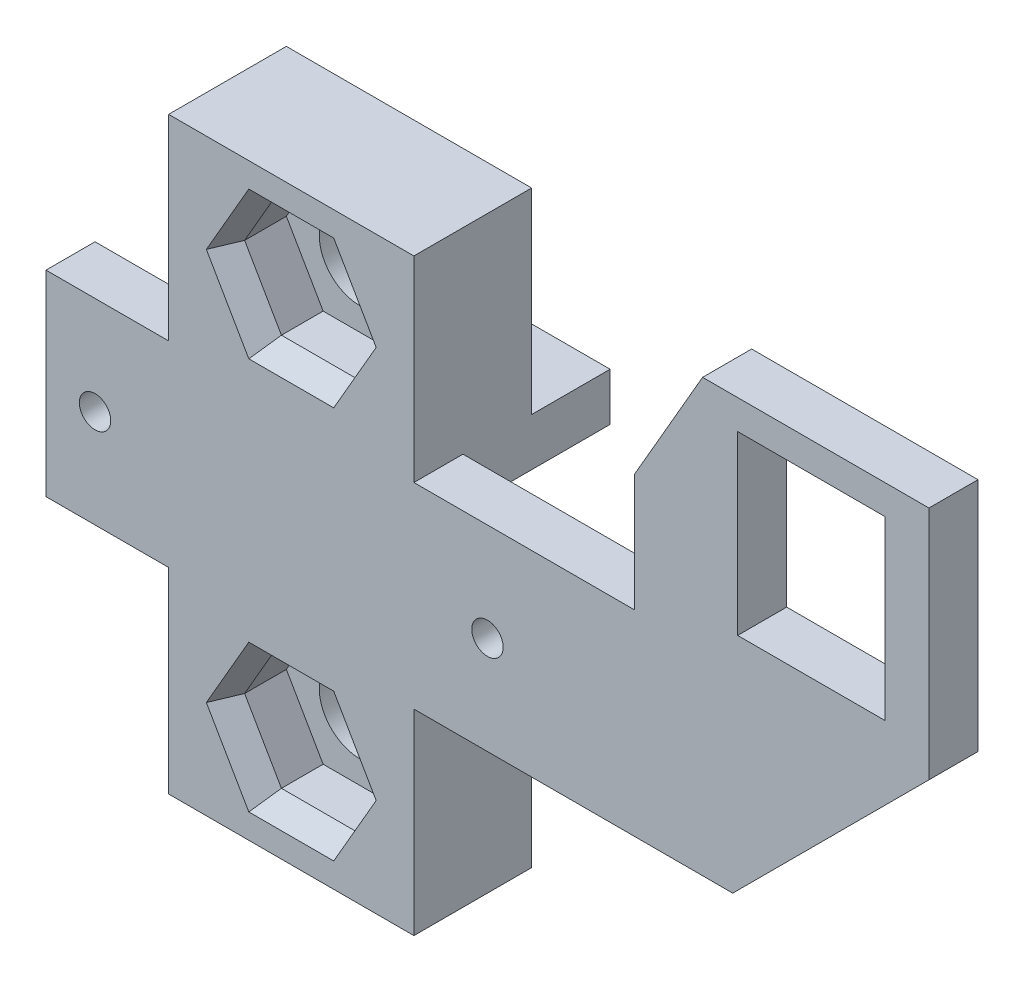
SolidWorks part; units mm, degrees
ref_plane "Спереди" through (0, 0, 0) normal (0, 0, 1) x (1, 0, 0)
ref_plane "Сверху" through (0, 0, 0) normal (0, 1, 0) x (1, 0, 0)
ref_plane "Справа" through (0, 0, 0) normal (1, 0, 0) x (0, 0, -1)
sketch "Sketch2" plane through (0, 0, 0) normal (0, 0, 1) x (1, 0, 0)
  line L1 (12.5, -10) -> (-12.5, -10)
  line L2 (12.5, -10) -> (12.5, 10)
  line L3 (12.5, 10) -> (-12.5, 10)
  line L4 (-12.5, -10) -> (-12.5, 10)
  line L5 (12.5, -10) -> (-12.5, 10) construction
  line L6 (12.5, 10) -> (-12.5, -10) construction
  point P0 (0, 0)
  dimension "D1" = 25
  dimension "D2" = 20
extrude "Boss-Extrude1" add sketch "Sketch2" along normal blind 30
sketch "Sketch3" plane through (-12.5, 0, 0) normal (-1, 0, 0) x (0, 0, 1)
  line L0 (30, 0) -> (0, 0) construction
  line L1 (30, 10) -> (30, -10) construction
  line L2 (0, 10) -> (0, -10) construction
  line L4 (4.875, -5.125) -> (25.125, -5.125)
  line L5 (4.875, -5.125) -> (4.875, 5.125)
  line L6 (4.875, 5.125) -> (25.125, 5.125)
  line L7 (25.125, -5.125) -> (25.125, 5.125)
  line L8 (4.875, -5.125) -> (25.125, 5.125) construction
  line L9 (4.875, 5.125) -> (25.125, -5.125) construction
  point P6 (15, 0)
  dimension "D1" = 10.25
  dimension "D2" = 20.25
extrude "Cut-Extrude1" cut sketch "Sketch3" against normal through all
sketch "Sketch4" plane through (0, 0, 30) normal (0, 0, 1) x (1, 0, 0)
  line L1 (25, -10) -> (-25, -10)
  line L2 (25, -10) -> (25, 10)
  line L3 (25, 10) -> (-25, 10)
  line L4 (-25, -10) -> (-25, 10)
  line L5 (25, -10) -> (-25, 10) construction
  line L6 (25, 10) -> (-25, -10) construction
  point P0 (0, 0)
  dimension "D1" = 20
  dimension "D2" = 50
extrude "Boss-Extrude2" add sketch "Sketch4" along normal blind 5
sketch "Sketch6" plane through (0, 0, 35) normal (0, 0, 1) x (1, 0, 0)
  line L0 (-25, 0) -> (25, 0) construction
  line L1 (-25, 10) -> (-25, -10) construction
  line L2 (25, -10) -> (25, 10) construction
  circle A0 centre (-20, 0) radius 1.6
  circle A1 centre (20, 0) radius 1.6
  point P10 (0, 0)
  dimension "D3" = 3.2
  dimension "D1" = 40
  dimension "D2" = 20
extrude "Cut-Extrude2" cut sketch "Sketch6" against normal through all
sketch "Sketch9" plane through (25, 0, 0) normal (1, 0, 0) x (0, 0, -1)
  line L0 (-35, 10) -> (-30, -10) construction
  line L2 (-30, 10) -> (-35, 10)
  line L3 (-30, 10) -> (-30, -10)
  line L4 (-30, -10) -> (-35, -10)
  line L5 (-35, 10) -> (-35, -10)
  line L6 (-30, 10) -> (-35, -10) construction
  line L7 (-30, -10) -> (-35, 10) construction
  point P4 (-32.5, 0)
extrude "Boss-Extrude3" add sketch "Sketch9" along normal blind 40
sketch "Sketch14" plane through (0, 0, 35) normal (0, 0, 1) x (1, 0, 0)
  line L0 (65, 10) -> (65, 34)
  line L1 (65, 34) -> (35, 34)
  line L2 (35, 34) -> (35, 10)
  line L3 (65, 10) -> (-25, 10) construction
  line L4 (35, 10) -> (65, 10)
  dimension "D1" = 30
  dimension "D2" = 24
extrude "Boss-Extrude5" add sketch "Sketch14" against normal up to vertex
sketch "Sketch19" plane through (0, 0, 35) normal (0, 0, 1) x (1, 0, 0)
  line L0 (35, 22) -> (65, 22) construction
  line L1 (35, 10) -> (65, 10) construction
  line L2 (35, 34) -> (35, 10) construction
  line L3 (60.5, 31) -> (45.5, 31)
  line L4 (60.5, 31) -> (60.5, 13)
  line L5 (60.5, 13) -> (45.5, 13)
  line L6 (45.5, 31) -> (45.5, 13)
  line L7 (60.5, 31) -> (45.5, 13) construction
  line L8 (65, 34) -> (65, -10) construction
  line L9 (60.5, 13) -> (45.5, 31) construction
  point P5 (53, 22)
  dimension "D1" = 15
  dimension "D2" = 18
  dimension "D3" = 12
extrude "Cut-Extrude5" cut sketch "Sketch19" against normal through all
chamfer "Chamfer1" distance 12 angle 30 1 edges at (35, 34, 32.5)
chamfer "Chamfer2" distance 20 angle 45 1 edges at (65, -10, 32.5)
sketch "Sketch20" plane through (0, 10, 0) normal (0, 1, 0) x (1, 0, 0)
  line L0 (0, 0) -> (0, -35) construction
  line L1 (12.5, 0) -> (-12.5, 0) construction
  line L2 (35, -35) -> (-25, -35) construction
  line L4 (-12.5, -26) -> (12.5, -26)
  line L5 (-12.5, -26) -> (-12.5, -35)
  line L6 (-12.5, -35) -> (12.5, -35)
  line L7 (12.5, -26) -> (12.5, -35)
  line L8 (-12.5, -26) -> (12.5, -35) construction
  line L9 (-12.5, -35) -> (12.5, -26) construction
  point P6 (0, -30.5)
  dimension "D1" = 9
extrude "Boss-Extrude6" add sketch "Sketch20" along normal blind 20 and the other way blind 40
sketch "Sketch21" plane through (0, 0, 0) normal (0, 0, -1) x (-1, 0, 0)
  line L0 (12.5, 0) -> (-12.5, 0) construction
  line L1 (12.5, 10) -> (12.5, -10) construction
  line L2 (-12.5, -10) -> (-12.5, 10) construction
  line L4 (-12.5, -10) -> (12.5, -10)
  line L5 (-12.5, -10) -> (-12.5, 10)
  line L6 (-12.5, 10) -> (12.5, 10)
  line L7 (12.5, -10) -> (12.5, 10)
  line L8 (-12.5, -10) -> (12.5, 10) construction
  line L9 (-12.5, 10) -> (12.5, -10) construction
  point P6 (0, 0)
extrude "Cut-Extrude6" cut sketch "Sketch21" against normal blind 15
sketch "Sketch22" plane through (0, 0, 35) normal (0, 0, 1) x (1, 0, 0)
  line L0 (0, 30) -> (0, -30) construction
  line L1 (-12.5, 30) -> (12.5, 30) construction
  line L2 (-12.5, -30) -> (12.5, -30) construction
  line L4 (7.5, 20) -> (3.75, 26.4952)
  line L5 (3.75, 26.4952) -> (-3.75, 26.4952)
  line L6 (-3.75, 26.4952) -> (-7.5, 20)
  line L7 (-7.5, 20) -> (-3.75, 13.5048)
  line L8 (-3.75, 13.5048) -> (3.75, 13.5048)
  line L9 (3.75, 13.5048) -> (7.5, 20)
  line L10 (7.5, -20) -> (3.75, -13.5048)
  line L11 (3.75, -13.5048) -> (-3.75, -13.5048)
  line L12 (-3.75, -13.5048) -> (-7.5, -20)
  line L13 (-7.5, -20) -> (-3.75, -26.4952)
  line L14 (-3.75, -26.4952) -> (3.75, -26.4952)
  line L15 (3.75, -26.4952) -> (7.5, -20)
  circle A0 centre (0, 20) radius 7.5 construction
  circle A1 centre (0, -20) radius 7.5 construction
  point P15 (0, 0)
  dimension "D1" = 40
  dimension "D3" = 15
  dimension "D2" = 20
extrude "Cut-Extrude7" cut sketch "Sketch22" against normal blind 7
sketch "Sketch23" plane through (0, 0, 26) normal (0, 0, -1) x (-1, 0, 0)
  line L0 (12.5, 20) -> (-12.5, 20) construction
  line L1 (12.5, 10) -> (12.5, 30) construction
  line L2 (-12.5, 10) -> (-12.5, 30) construction
  line L3 (12.5, -20) -> (-12.5, -20) construction
  line L4 (12.5, -30) -> (12.5, -10) construction
  line L5 (-12.5, -30) -> (-12.5, -10) construction
  line L7 (-12.5, 10) -> (12.5, 10)
  line L8 (-12.5, 10) -> (-12.5, 30)
  line L9 (-12.5, 30) -> (12.5, 30)
  line L10 (12.5, 10) -> (12.5, 30)
  line L11 (-12.5, 10) -> (12.5, 30) construction
  line L12 (-12.5, 30) -> (12.5, 10) construction
  line L13 (-12.5, -10) -> (12.5, -10)
  line L14 (-12.5, -10) -> (-12.5, -30)
  line L15 (-12.5, -30) -> (12.5, -30)
  line L16 (12.5, -10) -> (12.5, -30)
  line L17 (-12.5, -10) -> (12.5, -30) construction
  line L18 (-12.5, -30) -> (12.5, -10) construction
  point P12 (0, 20)
  point P18 (0, -20)
extrude "Boss-Extrude7" add sketch "Sketch23" along normal blind 3
sketch "Sketch24" plane through (0, 0, 28) normal (0, 0, 1) x (1, 0, 0)
  line L0 (7.5, 20) -> (-7.5, 20) construction
  line L1 (7.5, -20) -> (-7.5, -20) construction
  circle A0 centre (0, 20) radius 4.15
  circle A1 centre (0, -20) radius 4.15
  dimension "D1" = 8.3
extrude "Cut-Extrude8" cut sketch "Sketch24" against normal through all
chamfer "Chamfer3" distance 1 angle 70 12 edges at (0, 13.5048, 35) (-5.625, 16.7524, 35) (-5.625, 23.2476, 35) (0, 26.4952, 35) (5.625, 23.2476, 35) (5.625, 16.7524, 35) (-5.625, -23.2476, 35) (-5.625, -16.7524, 35) (0, -13.5048, 35) (5.625, -16.7524, 35) (5.625, -23.2476, 35) (0, -26.4952, 35)
